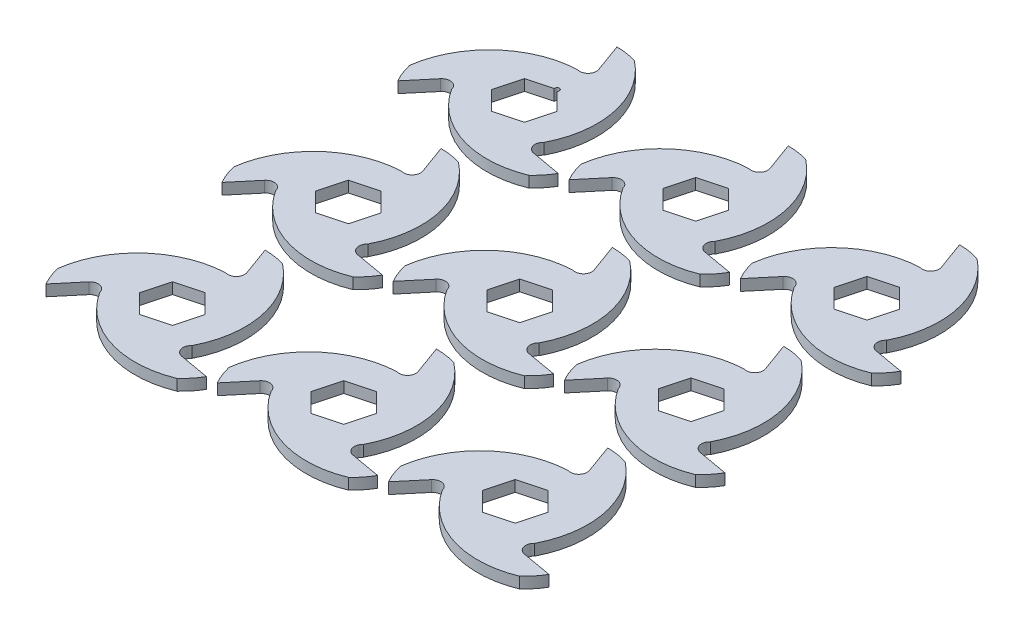
SolidWorks part; units mm, degrees
ref_plane "Front Plane" through (0, 0, 0) normal (0, 0, 1) x (1, 0, 0)
ref_plane "Top Plane" through (0, 0, 0) normal (0, 1, 0) x (1, 0, 0)
ref_plane "Right Plane" through (0, 0, 0) normal (1, 0, 0) x (0, 0, -1)
sketch "Sketch2" plane through (0, 0, 0) normal (0, 1, 0) x (1, 0, 0)
  line L0 (0, 50.8) -> (0, 0) construction
  line L1 (0, 0) -> (-43.9941, -25.4) construction
  line L2 (0, 0) -> (43.9941, -25.4) construction
  line L3 (0, 50.8) -> (5.6992, 35.1416)
  line L4 (43.9941, -25.4) -> (27.5839, -22.5064)
  line L5 (-43.9941, -25.4) -> (-33.2831, -12.6352)
  line L7 (3.7955, 14.165) -> (-10.3695, 10.3695)
  line L8 (-10.3695, 10.3695) -> (-14.165, -3.7955)
  line L9 (-14.165, -3.7955) -> (-3.7955, -14.165)
  line L10 (-3.7955, -14.165) -> (10.3695, -10.3695)
  line L11 (10.3695, -10.3695) -> (14.165, 3.7955)
  line L12 (14.165, 3.7955) -> (3.7955, 14.165)
  circle A0 centre (0, 0) radius 50.8 construction
  circle A1 centre (0, 13.2055) radius 37.5945
  circle A2 centre (11.4363, -6.6028) radius 37.5945
  circle A3 centre (-11.4363, -6.6028) radius 37.5945
  arc A4 (5.6992, 35.1416) -> (0, 29.21) centre (1.3938, 33.5746) cw
  arc A5 (27.5839, -22.5064) -> (25.2966, -14.605) centre (28.3796, -17.9943) cw
  arc A6 (-33.2831, -12.6352) -> (-25.2966, -14.605) centre (-29.7733, -15.5803) cw
  circle A7 centre (0, 0) radius 12.7 construction
  point P25 (0, 0)
  dimension "D1" = 101.6
  dimension "D4" = 20
  dimension "D6" = 15
  dimension "D2" = 120
  dimension "D3" = 120
  dimension "D5" = 21.59
  dimension "D8" = 25.4
  dimension "D7" = 3
extrude "Boss-Extrude2" add sketch "Sketch2" along normal mid plane 6.096 contours A1 A3 A2 L12 L11 L10 L9 L8 L7 | A1 A6 A2 A3 | L5 A6 A1 A3 | L4 A5 A3 A2 | A3 A5 A1 A2 | A2 A4 A3 A1 | L3 A4 A2 A1
sketch "Sketch3" plane through (0, 3.048, 0) normal (0, 1, 0) x (1, 0, 0)
  line L3 (43.9941, -25.4) -> (27.5839, -22.5064)
  line L4 (0, 50.8) -> (5.6992, 35.1416)
  line L5 (-43.9941, -25.4) -> (-33.2831, -12.6352)
  line L6 (43.9941, -25.4) -> (27.5839, -22.5064)
  line L7 (0, 50.8) -> (5.6992, 35.1416)
  line L8 (-43.9941, -25.4) -> (-33.2831, -12.6352)
  arc A0 (-48.1379, -14.7476) -> (0, 29.21) centre (2.2057, -21.5421) cw
  arc A1 (0, 29.21) -> (-43.9941, -25.4) centre (-11.4363, -6.6028) ccw construction
  arc A2 (0, 29.21) -> (5.6992, 35.1416) centre (1.3938, 33.5746) ccw construction
  arc A3 (11.2972, 49.0624) -> (25.2966, -14.605) centre (-19.7588, 8.8609) cw
  arc A4 (36.8407, -34.3148) -> (-25.2966, -14.605) centre (17.5532, 12.6812) cw
  arc A9 (-25.2966, -14.605) -> (-33.2831, -12.6352) centre (-29.7733, -15.5803) ccw
  arc A10 (-25.2966, -14.605) -> (43.9941, -25.4) centre (11.4363, -6.6028) ccw
  arc A11 (25.2966, -14.605) -> (27.5839, -22.5064) centre (28.3796, -17.9943) ccw
  arc A12 (25.2966, -14.605) -> (0, 50.8) centre (0, 13.2055) ccw
  arc A13 (0, 29.21) -> (5.6992, 35.1416) centre (1.3938, 33.5746) ccw
  arc A14 (0, 29.21) -> (-43.9941, -25.4) centre (-11.4363, -6.6028) ccw
  arc A15 (-25.2966, -14.605) -> (-33.2831, -12.6352) centre (-29.7733, -15.5803) ccw
  arc A16 (-25.2966, -14.605) -> (43.9941, -25.4) centre (11.4363, -6.6028) ccw
  arc A17 (25.2966, -14.605) -> (27.5839, -22.5064) centre (28.3796, -17.9943) ccw
  arc A18 (25.2966, -14.605) -> (0, 50.8) centre (0, 13.2055) ccw
  arc A19 (0, 29.21) -> (5.6992, 35.1416) centre (1.3938, 33.5746) ccw
  arc A20 (0, 29.21) -> (-43.9941, -25.4) centre (-11.4363, -6.6028) ccw
  point P26 (0, 0)
  arc M20 (-25.2966, -14.605) -> (43.9941, -25.4) centre (11.4363, -6.6028) ccw
  arc M23 (25.2966, -14.605) -> (0, 50.8) centre (0, 13.2055) ccw
  arc M26 (0, 29.21) -> (-43.9941, -25.4) centre (-11.4363, -6.6028) ccw
  dimension "D3" = 50.8
  dimension "D1" = 11.43
  dimension "D2" = 0
  dimension "D4" = 3
extrude "Cut-Extrude1" cut sketch "Sketch3" against normal through all contours A0 M26 | A3 M23 | A4 M20
pattern_linear "LPattern1" count 3 spacing 96.52 along (0, 0, 1) count 3 spacing 93.98 along (1, 0, 0) of "Boss-Extrude2"
sketch "Sketch4" plane through (0, 3.048, 0) normal (0, 1, 0) x (1, 0, 0)
  circle A0 centre (3.7955, 14.165) radius 1.27
  dimension "D1" = 2.54
extrude "Cut-Extrude2" cut sketch "Sketch4" against normal through all
